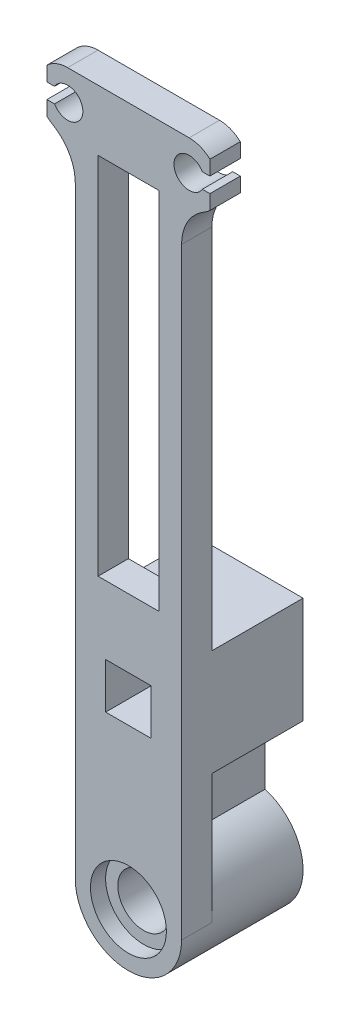
SolidWorks part; units mm, degrees
ref_plane "前视基准面" through (0, 0, 0) normal (0, 0, 1) x (1, 0, 0)
ref_plane "上视基准面" through (0, 0, 0) normal (0, 1, 0) x (1, 0, 0)
ref_plane "右视基准面" through (0, 0, 0) normal (1, 0, 0) x (0, 0, -1)
other "Configuration Table"
sketch "草图1" plane through (0, 0, 0) normal (0, 0, 1) x (1, 0, 0)
  line L0 (0, -1000) -> (0, 49000) construction
  line L1 (-1000, 0) -> (49000, 0) construction
  line L2 (-8.9461, 44) -> (9.1383, 44) construction
  line L3 (-2, 42) -> (2, 42)
  line L4 (-2, 42) -> (-2, 18)
  line L5 (-2, 18) -> (2, 18)
  line L6 (2, 42) -> (2, 18)
  line L7 (-2, 42) -> (2, 18) construction
  line L8 (-2, 18) -> (2, 42) construction
  line L9 (4, 46) -> (-4, 46)
  line L10 (-1.5, 13.5) -> (1.5, 13.5)
  line L11 (-1.5, 13.5) -> (-1.5, 10.5)
  line L12 (-1.5, 10.5) -> (1.5, 10.5)
  line L13 (1.5, 13.5) -> (1.5, 10.5)
  line L14 (-1.5, 13.5) -> (1.5, 10.5) construction
  line L15 (-1.5, 10.5) -> (1.5, 13.5) construction
  line L16 (-3.5, 42) -> (-3.5, 0)
  line L17 (3.5, 42) -> (3.5, 0)
  line L18 (-3.5, 42) -> (-3.5, 42.0635)
  line L19 (3.5, 42) -> (3.5, 42.0635)
  circle A0 centre (0, 0) radius 1.7
  circle A1 centre (-4, 44) radius 1
  circle A2 centre (4, 44) radius 1
  arc A3 (-3.5, 0) -> (3.5, 0) centre (0, 0) ccw
  arc A4 (-4, 46) -> (-3.5, 42.0635) centre (-4, 44) ccw
  arc A5 (4, 46) -> (3.5, 42.0635) centre (4, 44) cw
  point P3 (0, 30)
  point P18 (0, 12)
  point P28 (0, 46)
  dimension "D1" = 3.4
  dimension "D6" = 2
  dimension "D2" = 18
  dimension "D3" = 42
  dimension "D4" = 4
  dimension "D5" = 2
  dimension "D7" = 4
  dimension "D8" = 3
  dimension "D9" = 3
  dimension "D10" = 12
  dimension "D11" = 2
  dimension "D13" = 1.5
extrude "凸台-拉伸1" add sketch "草图1" along normal blind 2
sketch "草图2" plane through (0, 0, 0) normal (0, 0, -1) x (-1, 0, 0)
  line L0 (3.5, 42.0635) -> (3.5, 0) construction
  line L1 (-3.5, 15.5) -> (3.5, 15.5)
  line L2 (-3.5, 15.5) -> (-3.5, 8.5)
  line L3 (-3.5, 8.5) -> (3.5, 8.5)
  line L4 (3.5, 15.5) -> (3.5, 8.5)
  line L5 (-3.5, 15.5) -> (3.5, 8.5) construction
  line L6 (-3.5, 8.5) -> (3.5, 15.5) construction
  line L7 (-1.5, 10.5) -> (-1.5, 13.5) construction
  line L8 (-1.5, 13.5) -> (1.5, 13.5) construction
  line L9 (1.5, 13.5) -> (1.5, 10.5) construction
  line L10 (1.5, 10.5) -> (-1.5, 10.5) construction
  line L11 (-1.5, 10.5) -> (-1.5, 13.5)
  line L12 (-1.5, 13.5) -> (1.5, 13.5)
  line L13 (1.5, 13.5) -> (1.5, 10.5)
  line L14 (1.5, 10.5) -> (-1.5, 10.5)
  line L15 (0, -988) -> (0, 49012) construction
  line L16 (-1, 8.5) -> (-1, 3.3541)
  line L17 (1, 8.5) -> (1, 3.3541)
  circle A0 centre (0, 0) radius 3.5
  circle A1 centre (0, 0) radius 1.7
  point P4 (0, 12)
  line M10 (-3.5, 42.0635) -> (-3.5, 0)
  arc M11 (-3.5, 0) -> (3.5, 0) centre (0, 0) ccw
  line M12 (3.5, 0) -> (3.5, 42.0635)
  circle M15 centre (0, 0) radius 1.7
  line M21 (1.5, 10.5) -> (-1.5, 10.5)
  line M22 (-1.5, 10.5) -> (-1.5, 13.5)
  line M23 (-1.5, 13.5) -> (1.5, 13.5)
  line M24 (1.5, 13.5) -> (1.5, 10.5)
  dimension "D1" = 7
  dimension "D2" = 3.4
  dimension "D3" = 7
  dimension "D4" = 7
  dimension "D5" = 12
  dimension "D6" = 1
extrude "凸台-拉伸2" add sketch "草图2" along normal blind 6 contours L3 L1 M10 M12 M24 M21 M22 M23 | A0 L17 L3 L16 | A0 M11 M15
fillet "圆角2" radius 3 2 edges at (-3.5, 42.0635, 1) (3.5, 42.0635, 1)
sketch "草图3" plane through (0, 0, 2) normal (0, 0, 1) x (1, 0, 0)
  line L0 (-1004, 44) -> (-5, 44) construction
  line L1 (-5.9365, 43.5) -> (-4.866, 43.5)
  line L2 (-5.9365, 44.5) -> (-4.866, 44.5)
  line L3 (0, -958) -> (0, 49042) construction
  line L4 (2, 42) -> (-2, 42) construction
  line L5 (-3, 44) -> (48996, 44) construction
  line L6 (5.9365, 44.5) -> (4.866, 44.5)
  line L7 (5.9365, 43.5) -> (4.866, 43.5)
  line L8 (-5.366, 43.5) -> (-5.366, 44.5)
  line L9 (-5.366, 44.5) -> (-5.366, 45.4608)
  line L10 (-5.366, 43.5) -> (-5.366, 42.5392)
  line L11 (5.366, 43.5) -> (5.366, 44.5)
  line L12 (5.366, 43.5) -> (5.366, 42.5392)
  line L13 (5.366, 44.5) -> (5.366, 45.4608)
  circle A0 centre (-4, 44) radius 1 construction
  arc A1 (-4, 46) -> (-5, 42.2679) centre (-4, 44) ccw construction
  arc A2 (-4.866, 44.5) -> (-4.866, 43.5) centre (-4, 44) ccw
  arc A3 (-5.9365, 44.5) -> (-5.9365, 43.5) centre (-4, 44) ccw
  arc A4 (4.866, 44.5) -> (4.866, 43.5) centre (4, 44) cw
  arc A5 (5.9365, 44.5) -> (5.9365, 43.5) centre (4, 44) cw
  arc A6 (-5.366, 45.4608) -> (-5.366, 42.5392) centre (-4, 44) ccw
  arc A7 (5.366, 45.4608) -> (5.366, 42.5392) centre (4, 44) cw
  point P17 (0, 42)
  circle M7 centre (4, 44) radius 1
  circle M8 centre (-4, 44) radius 1
  arc M15 (5, 42.2679) -> (4, 46) centre (4, 44) ccw
  arc M17 (-4, 46) -> (-5, 42.2679) centre (-4, 44) ccw
  dimension "D1" = 0.5
  dimension "D2" = 0.5
sketch "草图4" plane through (0, 0, 2) normal (0, 0, 1) x (1, 0, 0)
  circle A0 centre (0, 0) radius 2.5
  dimension "D1" = 5
extrude "切除-拉伸2" cut sketch "草图4" against normal blind 1
sketch "草图5" plane through (0, 0, -6) normal (0, 0, -1) x (-1, 0, 0)
  circle A0 centre (0, 0) radius 2.5
  dimension "D1" = 5
extrude "切除-拉伸3" cut sketch "草图5" against normal blind 1
extrude "切除-拉伸4" cut sketch "草图3" against normal blind 10 contours L8 L1 L2 M8 | L1 L8 L2 M17 | L2 L9 M17 | L10 L1 M17 | L11 L7 L6 M15 | L13 L6 M15 | L7 L11 L6 M7 | L7 L12 M15
ref_plane "基准面1" through (0, 30, 0) normal (0, 1, 0) x (1, 0, 0)
